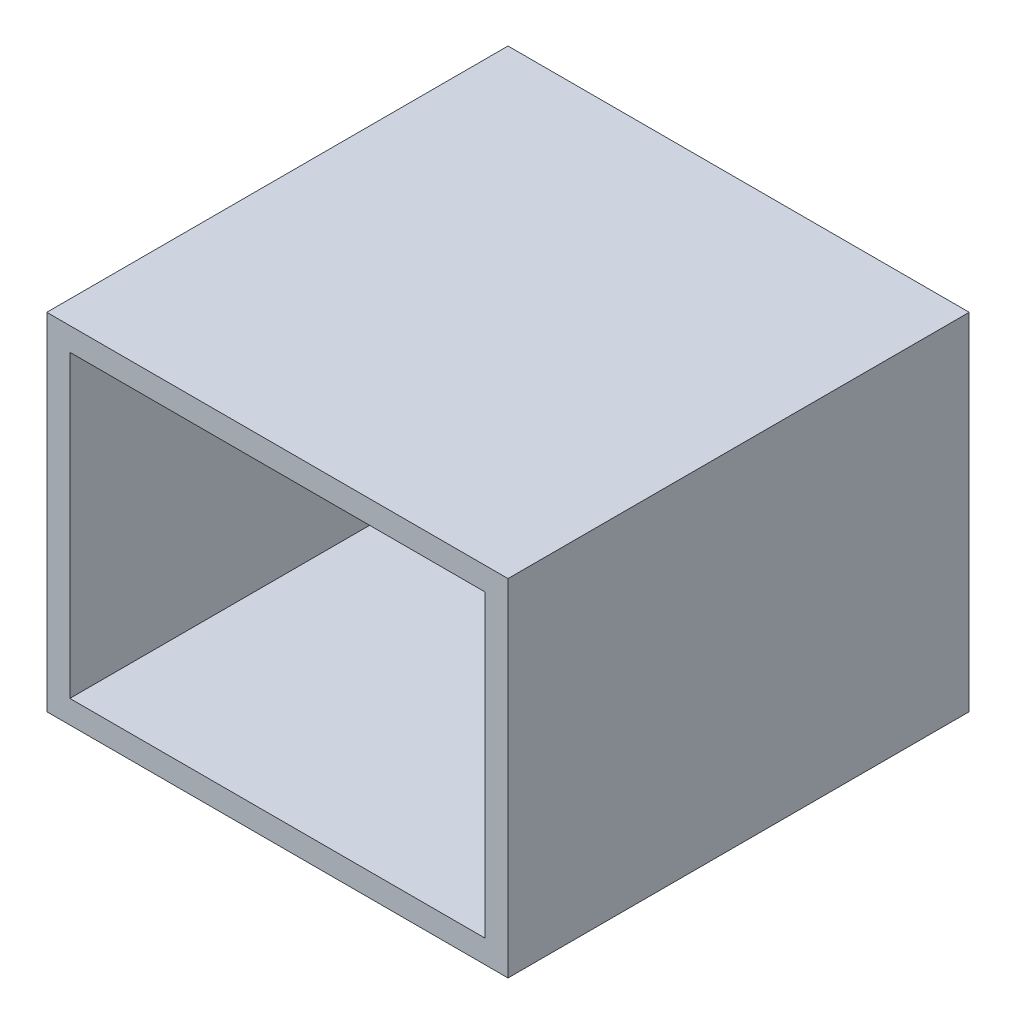
SolidWorks part; units mm, degrees
ref_plane "Plan de face" through (0, 0, 0) normal (0, 0, 1) x (1, 0, 0)
ref_plane "Plan de dessus" through (0, 0, 0) normal (0, 1, 0) x (1, 0, 0)
ref_plane "Plan de droite" through (0, 0, 0) normal (1, 0, 0) x (0, 0, -1)
sketch "Esquisse1" plane through (0, 0, 0) normal (0, 0, 1) x (1, 0, 0)
  line L1 (0, 0) -> (200, 0)
  line L2 (0, 0) -> (0, 150)
  line L3 (0, 150) -> (200, 150)
  line L4 (200, 0) -> (200, 150)
  line L5 (10, 10) -> (190, 10)
  line L6 (10, 10) -> (10, 140)
  line L7 (10, 140) -> (190, 140)
  line L8 (190, 10) -> (190, 140)
  dimension "D1" = 150
  dimension "D2" = 200
  dimension "D3" = 10
  dimension "D4" = 10
  dimension "D5" = 10
  dimension "D6" = 10
extrude "Boss.-Extru.1" add sketch "Esquisse1" along normal blind 200
